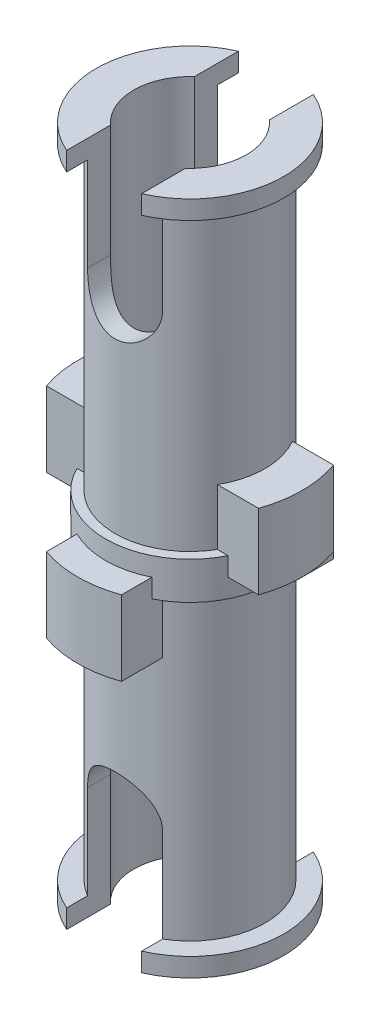
SolidWorks part; units mm, degrees
material "PBT General Purpose"
ref_plane "Front Plane" through (0, 0, 0) normal (0, 0, 1) x (1, 0, 0)
ref_plane "Top Plane" through (0, 0, 0) normal (0, 1, 0) x (1, 0, 0)
ref_plane "Right Plane" through (0, 0, 0) normal (1, 0, 0) x (0, 0, -1)
sketch "Sketch1" plane through (0, 0, 0) normal (0, 0, 1) x (1, 0, 0)
  line L0 (0, 9) -> (0, -9) construction
  line L1 (-2, 9) -> (0, 9)
  line L3 (-2, -9) -> (-2, 9)
  line L6 (-2, -9) -> (0, -9)
  line L7 (0, 9) -> (0, -9)
  line L9 (0, 9) -> (-2.5, 9)
  line L10 (0, 9) -> (0, 8.5)
  line L11 (0, 8.5) -> (-2.5, 8.5)
  line L12 (-2.5, 9) -> (-2.5, 8.5)
  line L13 (0, -9) -> (-2.5, -9)
  line L14 (0, -9) -> (0, -8.5)
  line L15 (0, -8.5) -> (-2.5, -8.5)
  line L16 (-2.5, -9) -> (-2.5, -8.5)
  line L17 (0, -0.5) -> (-2.25, -0.5)
  line L18 (0, -0.5) -> (0, 0.5)
  line L19 (0, 0.5) -> (-2.25, 0.5)
  line L20 (-2.25, -0.5) -> (-2.25, 0.5)
  point P3 (0, 0)
  point P16 (0, 0)
  dimension "D1" = 18
  dimension "D2" = 2
  dimension "D3" = 2.5
  dimension "D4" = 0.5
  dimension "D5" = 1
  dimension "D6" = 2.25
revolve "Revolve5" add sketch "Sketch1" angle 360 about L0
sketch "Sketch3" plane through (0, 0, 0) normal (0, 0, 1) x (1, 0, 0)
  line L0 (2.25, 0) -> (-2.25, 0) construction
  line L1 (2.25, -0.5) -> (2.25, 0.5) construction
  line L2 (-2.25, 0.5) -> (-2.25, -0.5) construction
  line L4 (-3, 0) -> (3, 0)
  line L5 (-3, 0) -> (-3, 2)
  line L6 (-3, 2) -> (3, 2)
  line L7 (3, 0) -> (3, 2)
  line L8 (2, 0.5) -> (2, 8.5) construction
  dimension "D1" = 2
  dimension "D2" = 6
  dimension "D3" = 1
extrude "Boss-Extrude4" add sketch "Sketch3" along normal mid plane 2
sketch "Sketch4" plane through (0, 0, 0) normal (1, 0, 0) x (0, 0, -1)
  line L0 (-2.25, 0) -> (2.25, 0) construction
  line L1 (-2.25, 0.5) -> (-2.25, -0.5) construction
  line L2 (2.25, -0.5) -> (2.25, 0.5) construction
  line L3 (-2, 8.5) -> (-2, 0.5) construction
  line L4 (-3, -2) -> (3, -2)
  line L5 (-3, -2) -> (-3, 0)
  line L6 (-3, 0) -> (3, 0)
  line L7 (3, -2) -> (3, 0)
  dimension "D1" = 6
  dimension "D2" = 2
  dimension "D3" = 1
extrude "Boss-Extrude5" add sketch "Sketch4" along normal mid plane 2
sketch "Sketch5" plane through (0, 0, 0) normal (0, 0, 1) x (1, 0, 0)
  line L0 (-1, 9) -> (-1, 6)
  line L1 (2.5, 9) -> (-2.5, 9) construction
  line L2 (1, 6) -> (1, 9)
  line L3 (1, 9) -> (-1, 9)
  line L8 (-1, -9) -> (-1, -6)
  line L9 (-2.5, -9) -> (2.5, -9) construction
  line L10 (1, -6) -> (1, -9)
  line L11 (1, -9) -> (-1, -9)
  arc A0 (-1, 6) -> (1, 6) centre (0, 6) ccw
  arc A2 (-1, -6) -> (1, -6) centre (0, -6) cw
  dimension "D1" = 1
  dimension "D2" = 3
extrude "Cut-Extrude2" cut sketch "Sketch5" against normal through all both and the other way through all
sketch "Sketch6" plane through (0, 9, 0) normal (0, 1, 0) x (1, 0, 0)
  circle A0 centre (0, 0) radius 1.5
  dimension "D1" = 3
extrude "Cut-Extrude3" cut sketch "Sketch6" against normal up to surface (18 mm away) up to face at (-1.75, -9, 0)
sketch "Sketch7" plane through (0, 0, 0) normal (0, 1, 0) x (1, 0, 0)
  circle A1 centre (0, 0) radius 3
  dimension "D1" = 6
extrude "Cut-Extrude4" cut sketch "Sketch7" against normal through all both and the other way through all flip side to cut
